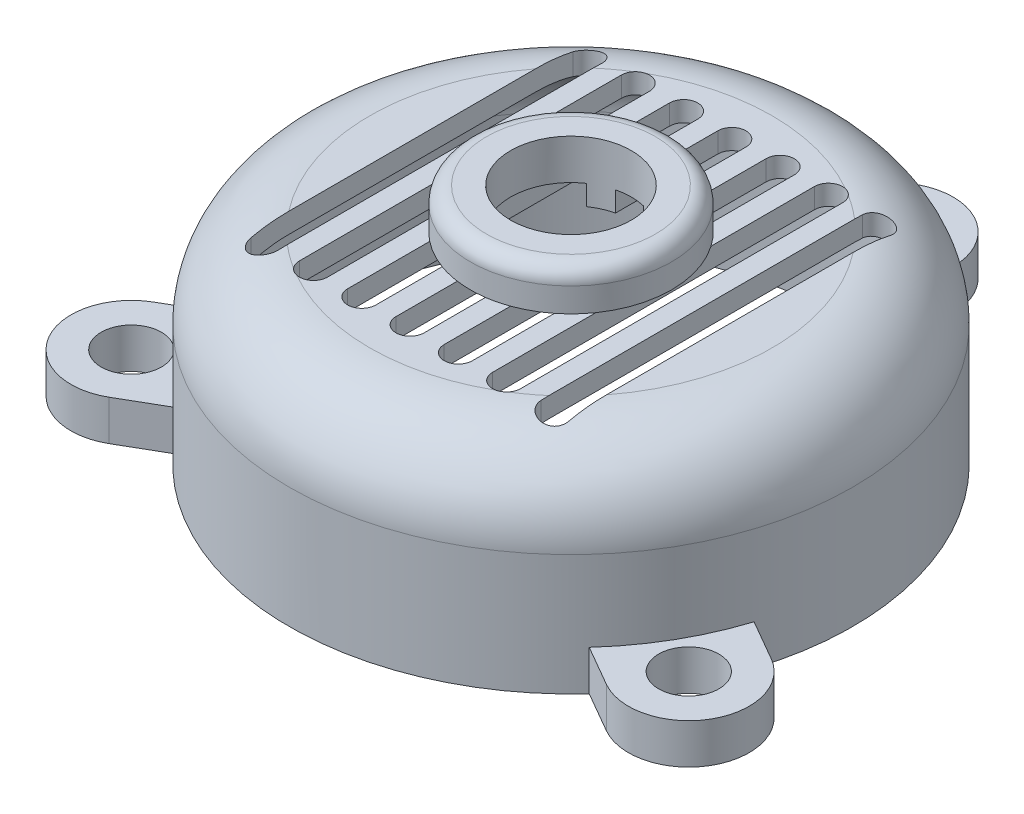
SolidWorks part; units mm, degrees
ref_plane "Front Plane" through (0, 0, 0) normal (0, 0, 1) x (1, 0, 0)
ref_plane "Top Plane" through (0, 0, 0) normal (0, 1, 0) x (1, 0, 0)
ref_plane "Right Plane" through (0, 0, 0) normal (1, 0, 0) x (0, 0, -1)
sketch "Sketch1" plane through (0, 0, 0) normal (0, 0, 1) x (1, 0, 0)
  line L0 (0, 0) -> (0, 13.3795) construction
  line L2 (-3.5, 0) -> (-3.5, 1.5)
  line L3 (-2.5, 2.5) -> (0, 2.5)
  line L5 (0, 2.5) -> (0, 0)
  line L6 (0, 0) -> (-3.5, 0)
  arc A1 (-3.5, 1.5) -> (-2.5, 2.5) centre (-2.5, 1.5) cw
  dimension "D6" = 1
  dimension "D1" = 3.5
  dimension "D2" = 2.5
revolve "Revolve1" add sketch "Sketch1" angle 360 about L0
shell "Shell1" thickness 0.25
sketch "Sketch2" plane through (0, 0, 0) normal (0, 1, 0) x (1, 0, 0)
  circle A0 centre (0, 0) radius 1.25
  dimension "D1" = 2.5
extrude "Boss-Extrude2" add sketch "Sketch2" along normal blind 0.75 from surface at 2.25 starting at face at (0, 2.25, -2.5)
sketch "Sketch4" plane through (0, 3, 0) normal (0, 1, 0) x (1, 0, 0)
  circle A0 centre (0, 0) radius 0.75
  dimension "D1" = 1.5
extrude "Cut-Extrude1" cut sketch "Sketch4" against normal blind 1
fillet "Fillet1" radius 0.2 1 edges at (0, 3, -1.25)
sketch "Sketch5" plane through (0, 0, 0) normal (0, 1, 0) x (1, 0, 0)
  line L0 (1.8, 2) -> (1.8, -2) construction
  line L1 (1.975, 2) -> (1.975, -2)
  line L2 (1.625, 2) -> (1.625, -2)
  line L3 (1.2, 2) -> (1.2, -2) construction
  line L4 (1.375, 2) -> (1.375, -2)
  line L5 (1.025, 2) -> (1.025, -2)
  line L6 (0.6, 2) -> (0.6, -2) construction
  line L7 (0.775, 2) -> (0.775, -2)
  line L8 (0.425, 2) -> (0.425, -2)
  line L9 (0, 2) -> (0, -2) construction
  line L10 (0.175, 2) -> (0.175, -2)
  line L11 (-0.175, 2) -> (-0.175, -2)
  line L12 (-0.6, 2) -> (-0.6, -2) construction
  line L13 (-0.425, 2) -> (-0.425, -2)
  line L14 (-0.775, 2) -> (-0.775, -2)
  line L15 (-1.2, 2) -> (-1.2, -2) construction
  line L16 (-1.025, 2) -> (-1.025, -2)
  line L17 (-1.375, 2) -> (-1.375, -2)
  line L18 (-1.8, 2) -> (-1.8, -2) construction
  line L19 (-1.625, 2) -> (-1.625, -2)
  line L20 (-1.975, 2) -> (-1.975, -2)
  arc A0 (1.975, 2) -> (1.625, 2) centre (1.8, 2) ccw
  arc A1 (1.625, -2) -> (1.975, -2) centre (1.8, -2) ccw
  arc A2 (1.375, 2) -> (1.025, 2) centre (1.2, 2) ccw
  arc A3 (1.025, -2) -> (1.375, -2) centre (1.2, -2) ccw
  arc A4 (0.775, 2) -> (0.425, 2) centre (0.6, 2) ccw
  arc A5 (0.425, -2) -> (0.775, -2) centre (0.6, -2) ccw
  arc A6 (0.175, 2) -> (-0.175, 2) centre (0, 2) ccw
  arc A7 (-0.175, -2) -> (0.175, -2) centre (0, -2) ccw
  arc A8 (-0.425, 2) -> (-0.775, 2) centre (-0.6, 2) ccw
  arc A9 (-0.775, -2) -> (-0.425, -2) centre (-0.6, -2) ccw
  arc A10 (-1.025, 2) -> (-1.375, 2) centre (-1.2, 2) ccw
  arc A11 (-1.375, -2) -> (-1.025, -2) centre (-1.2, -2) ccw
  arc A12 (-1.625, 2) -> (-1.975, 2) centre (-1.8, 2) ccw
  arc A13 (-1.975, -2) -> (-1.625, -2) centre (-1.8, -2) ccw
  point P2 (1.8, 0)
  point P11 (1.2, 0)
  point P18 (0.6, 0)
  point P25 (0, 0)
  point P32 (-0.6, 0)
  point P39 (-1.2, 0)
  point P46 (-1.8, 0)
  dimension "D1" = 4
  dimension "D2" = 0.35
  dimension "D3" = 1.8
  dimension "D5" = 0.6
  dimension "D4" = 7
extrude "Cut-Extrude2" cut sketch "Sketch5" against normal blind 1 from surface at 2.5 starting at face at (0, 2.5, -1.25)
sketch "Sketch6" plane through (0, 0, 0) normal (0, 1, 0) x (1, 0, 0)
  line L0 (-0.75, 4) -> (-0.75, 3.4187)
  line L1 (0.75, 4) -> (0.75, 3.4187)
  circle A0 centre (0, 0) radius 4 construction
  arc A1 (0.75, 4) -> (-0.75, 4) centre (0, 4) ccw
  circle A2 centre (0, 0) radius 3.5 construction
  arc A3 (0.75, 3.4187) -> (-0.75, 3.4187) centre (0, 0) ccw
  circle A4 centre (0, 4) radius 0.375
  dimension "D1" = 4
  dimension "D2" = 1.5
  dimension "D3" = 0.75
extrude "Boss-Extrude3" add sketch "Sketch6" along normal blind 0.5
pattern_circular "CirPattern2" count 3 over 360 about axis through (0, 0, 0) along (0, 1, 0) of "Boss-Extrude3"
